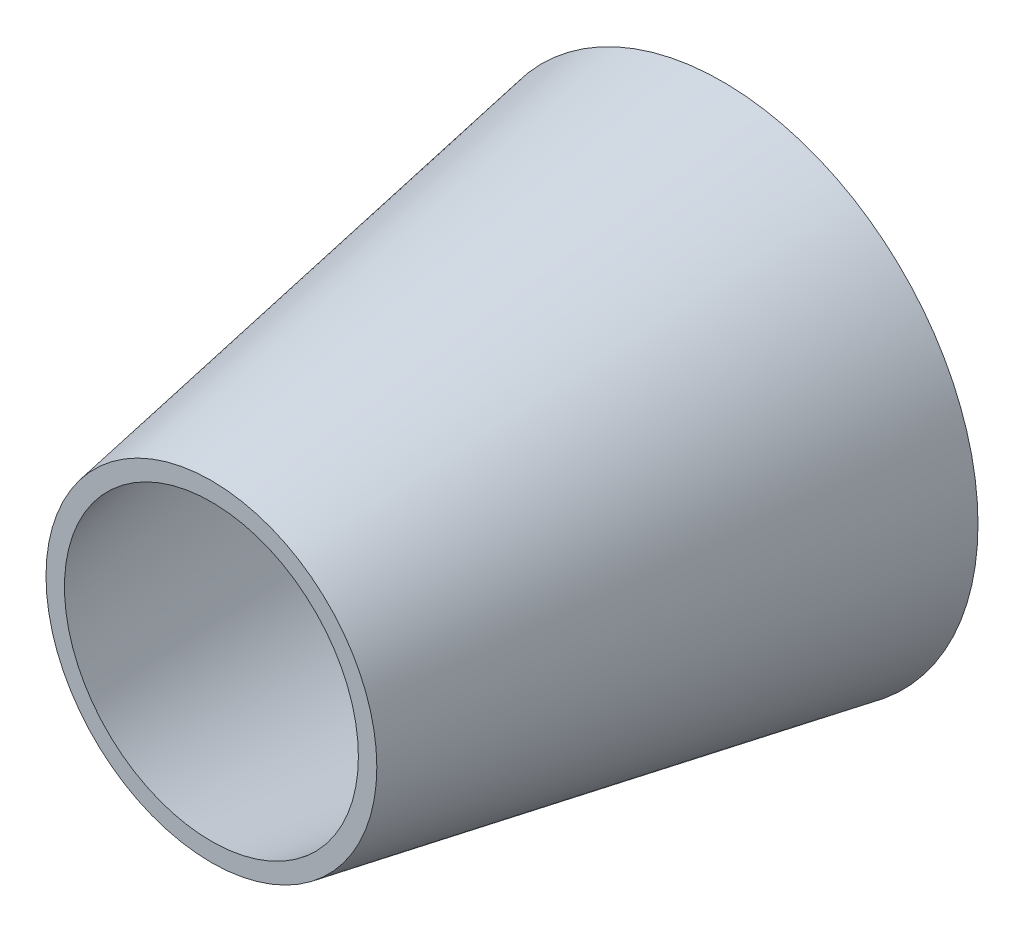
SolidWorks part; units mm, degrees
ref_plane "Front Plane" through (0, 0, 0) normal (0, 0, 1) x (1, 0, 0)
ref_plane "Top Plane" through (0, 0, 0) normal (0, 1, 0) x (1, 0, 0)
ref_plane "Right Plane" through (0, 0, 0) normal (1, 0, 0) x (0, 0, -1)
sketch "Sketch2" plane through (0, 0, 0) normal (0, 0, 1) x (1, 0, 0)
  circle A0 centre (0, 0) radius 15
extrude "Boss-Extrude1" add sketch "Sketch2" along normal blind 30 draft 10 contours A0
sketch "Sketch3" plane through (0, 0, 30) normal (0, 0, 1) x (1, 0, 0)
  circle A0 centre (0, 0) radius 8.6282
extrude "Cut-Extrude1" cut sketch "Sketch3" against normal blind 30 draft 9 draft outward yes
